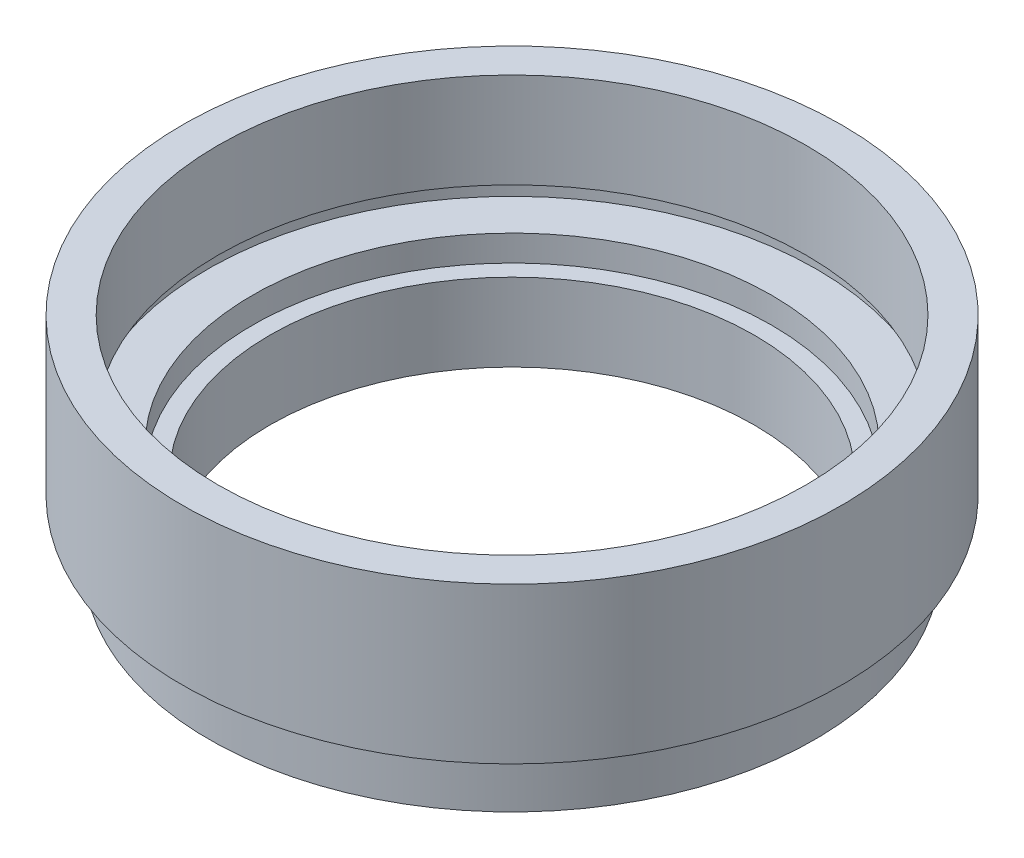
SolidWorks part; units mm, degrees
ref_plane "前视基准面" through (0, 0, 0) normal (0, 0, 1) x (1, 0, 0)
ref_plane "上视基准面" through (0, 0, 0) normal (0, 1, 0) x (1, 0, 0)
ref_plane "右视基准面" through (0, 0, 0) normal (1, 0, 0) x (0, 0, -1)
sketch "草图1" plane through (0, 0, 0) normal (0, 0, 1) x (1, 0, 0)
  line L0 (0, 0) -> (0, 21.8535) construction
  line L1 (14, 0) -> (17.5, 0)
  line L2 (17.5, 0) -> (17.5, 2.5)
  line L3 (17.5, 2.5) -> (17, 2.5)
  line L4 (17, 2.5) -> (17, 3.5)
  line L5 (17, 3.5) -> (19.05, 3.5)
  line L6 (19.05, 3.5) -> (19.05, 12.5)
  line L7 (19.05, 12.5) -> (17, 12.5)
  line L8 (17, 12.5) -> (17, 7)
  line L9 (17, 7) -> (17.6, 7)
  line L10 (17.6, 7) -> (17.6, 6)
  line L11 (17.6, 6) -> (15, 6)
  line L12 (15, 6) -> (15, 4.5)
  line L13 (15, 4.5) -> (14, 4.5)
  line L14 (14, 0) -> (14, 4.5)
  dimension "D1" = 12.5
  dimension "D2" = 19.05
  dimension "D3" = 17
  dimension "D4" = 15
  dimension "D5" = 1
  dimension "D6" = 1.5
  dimension "D7" = 14
  dimension "D8" = 17.5
  dimension "D9" = 1
  dimension "D10" = 3.5
  dimension "D11" = 4.5
  dimension "D12" = 17.6
  dimension "D13" = 17
revolve "旋转1" add sketch "草图1" angle 360 about L0
cosmetic thread "装饰螺纹线11" parameters "D2"=34
cosmetic thread "装饰螺纹线12" parameters "D2"=35
